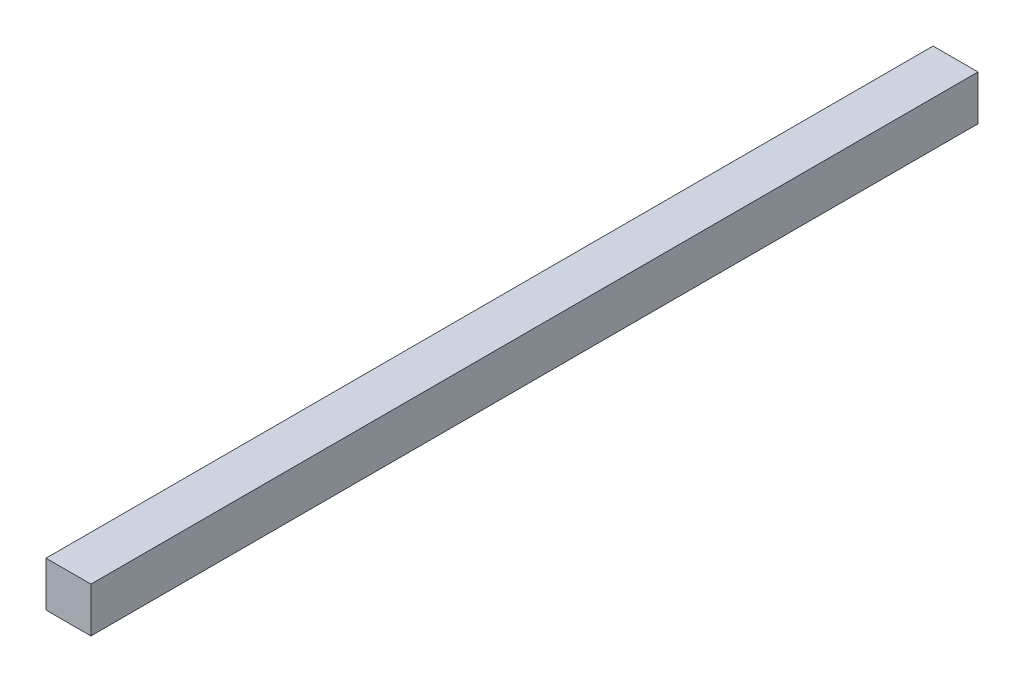
SolidWorks part; units mm, degrees
ref_plane "Płaszczyzna przednia" through (0, 0, 0) normal (0, 0, 1) x (1, 0, 0)
ref_plane "Płaszczyzna górna" through (0, 0, 0) normal (0, 1, 0) x (1, 0, 0)
ref_plane "Płaszczyzna prawa" through (0, 0, 0) normal (1, 0, 0) x (0, 0, -1)
sketch "Szkic1" plane through (0, 0, 0) normal (0, 0, 1) x (1, 0, 0)
  line L1 (0, 0) -> (20, 0)
  line L2 (0, 0) -> (0, 20)
  line L3 (0, 20) -> (20, 20)
  line L4 (20, 0) -> (20, 20)
  dimension "D1" = 20
  dimension "D2" = 20
extrude "Dodanie-wyciągnięcie1" add sketch "Szkic1" against normal blind 395
